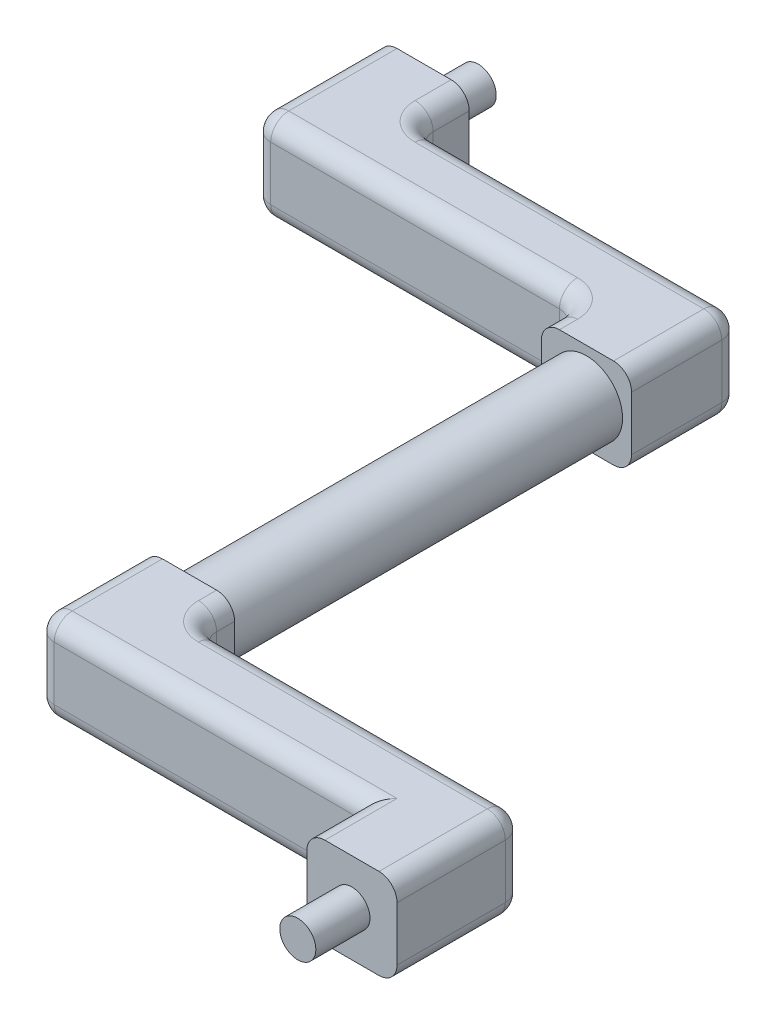
SolidWorks part; units mm, degrees
ref_plane "Alzado" through (0, 0, 0) normal (0, 0, 1) x (1, 0, 0)
ref_plane "Planta" through (0, 0, 0) normal (0, 1, 0) x (1, 0, 0)
ref_plane "Vista lateral" through (0, 0, 0) normal (1, 0, 0) x (0, 0, -1)
sketch "Croquis3" plane through (0, 0, 0) normal (0, 0, 1) x (1, 0, 0)
  circle A0 centre (0, 0) radius 12.7
  dimension "D1" = 25.4
extrude "Saliente-Extruir1" add sketch "Croquis3" against normal blind 88.9 and the other way blind 50.8
sketch "Croquis4" plane through (0, 0, -88.9) normal (0, 0, -1) x (-1, 0, 0)
  line L5 (-15.875, 15.875) -> (15.875, 15.875)
  line L6 (-15.875, 15.875) -> (-15.875, -15.875)
  line L7 (-15.875, -15.875) -> (15.875, -15.875)
  line L8 (15.875, 15.875) -> (15.875, -15.875)
  line L9 (-15.875, 15.875) -> (15.875, -15.875) construction
  line L10 (-15.875, -15.875) -> (15.875, 15.875) construction
  point P0 (0, 0)
  point P1 (0, 0)
  dimension "D1" = 31.75
  dimension "D2" = 31.75
extrude "Saliente-Extruir2" add sketch "Croquis4" along normal blind 38.1
sketch "Croquis6" plane through (-15.875, 0, 0) normal (-1, 0, 0) x (0, 0, 1)
  line L0 (-127, 15.875) -> (-88.9, 15.875) construction
  line L1 (-127, -15.875) -> (-101.6, -15.875)
  line L2 (-127, -15.875) -> (-127, 15.875)
  line L3 (-127, 15.875) -> (-101.6, 15.875)
  line L4 (-101.6, -15.875) -> (-101.6, 15.875)
  dimension "D1" = 25.4
extrude "Saliente-Extruir3" add sketch "Croquis6" along normal blind 114.3
sketch "Croquis8" plane through (0, 0, -127) normal (0, 0, -1) x (-1, 0, 0)
  line L0 (130.175, 15.875) -> (15.875, 15.875) construction
  line L1 (130.175, -15.875) -> (98.425, -15.875)
  line L2 (130.175, -15.875) -> (130.175, 15.875)
  line L3 (130.175, 15.875) -> (98.425, 15.875)
  line L4 (98.425, -15.875) -> (98.425, 15.875)
  dimension "D1" = 31.75
extrude "Saliente-Extruir4" add sketch "Croquis8" along normal blind 19.05
sketch "Croquis9" plane through (0, 0, -146.05) normal (0, 0, -1) x (-1, 0, 0)
  line L0 (130.175, 15.875) -> (98.425, 15.875) construction
  line L1 (98.425, 15.875) -> (98.425, -15.875) construction
  line L2 (98.425, 0) -> (130.175, 0) construction
  line L3 (130.175, -15.875) -> (130.175, 15.875) construction
  line L4 (114.3, 15.875) -> (114.3, -15.875) construction
  line L5 (98.425, -15.875) -> (130.175, -15.875) construction
  circle A0 centre (114.3, 0) radius 6.35
  dimension "D1" = 12.7
extrude "Saliente-Extruir5" add sketch "Croquis9" along normal blind 19.05
fillet "Redondeo1" radius 6.35 16 edges at (-98.425, -15.875, -136.525) (-15.875, -15.875, -95.25) (-98.425, 15.875, -136.525) (-130.175, 15.875, -123.825) (-130.175, -15.875, -123.825) (-41.275, -15.875, -127) (-73.025, -15.875, -101.6) (-41.275, 15.875, -127) (-130.175, 0, -101.6) (-98.425, 0, -127) (-15.875, 0, -101.6) (15.875, 0, -127) (15.875, 15.875, -107.95) (15.875, -15.875, -107.95) (-73.025, 15.875, -101.6) (-15.875, 15.875, -95.25)
ref_plane "Plano1" through (0, 0, -76.2) normal (0, 0, 1) x (1, 0, 0)
sketch "Croquis12" plane through (0, 0, 50.8) normal (0, 0, 1) x (1, 0, 0)
  line L1 (-15.875, 15.875) -> (15.875, 15.875)
  line L2 (-15.875, 15.875) -> (-15.875, -15.875)
  line L3 (-15.875, -15.875) -> (15.875, -15.875)
  line L4 (15.875, 15.875) -> (15.875, -15.875)
  line L5 (-15.875, 15.875) -> (15.875, -15.875) construction
  line L6 (-15.875, -15.875) -> (15.875, 15.875) construction
  point P0 (0, 0)
  dimension "D1" = 31.75
  dimension "D2" = 31.75
extrude "Saliente-Extruir6" add sketch "Croquis12" along normal blind 38.1
sketch "Croquis13" plane through (15.875, 0, 0) normal (1, 0, 0) x (0, 0, -1)
  line L0 (-88.9, -15.875) -> (-50.8, -15.875) construction
  line L1 (-88.9, 15.875) -> (-63.5, 15.875)
  line L2 (-88.9, 15.875) -> (-88.9, -15.875)
  line L3 (-88.9, -15.875) -> (-63.5, -15.875)
  line L4 (-63.5, 15.875) -> (-63.5, -15.875)
  dimension "D1" = 25.4
extrude "Saliente-Extruir7" add sketch "Croquis13" along normal blind 114.3
sketch "Croquis14" plane through (0, 0, 88.9) normal (0, 0, 1) x (1, 0, 0)
  line L0 (-15.875, -15.875) -> (130.175, -15.875) construction
  line L1 (130.175, 15.875) -> (98.425, 15.875)
  line L2 (130.175, 15.875) -> (130.175, -15.875)
  line L3 (130.175, -15.875) -> (98.425, -15.875)
  line L4 (98.425, 15.875) -> (98.425, -15.875)
  dimension "D1" = 31.75
extrude "Saliente-Extruir8" add sketch "Croquis14" along normal blind 19.05
sketch "Croquis16" plane through (0, 0, 107.95) normal (0, 0, 1) x (1, 0, 0)
  line L0 (98.425, 0) -> (134.9944, 0) construction
  line L1 (98.425, 15.875) -> (98.425, -15.875) construction
  line L2 (114.3, 15.875) -> (114.3, -24.0662) construction
  line L3 (130.175, 15.875) -> (98.425, 15.875) construction
  circle A0 centre (114.3, 0) radius 6.35
  dimension "D1" = 12.7
extrude "Saliente-Extruir9" add sketch "Croquis16" along normal blind 19.05
fillet "Redondeo2" radius 6.35 15 edges at (15.875, 0, 63.5) (-15.875, 15.875, 69.85) (-15.875, -15.875, 69.85) (-15.875, 0, 88.9) (41.275, -15.875, 88.9) (98.425, -15.875, 98.425) (98.425, 15.875, 98.425) (130.175, -15.875, 85.725) (130.175, 15.875, 85.725) (73.025, 15.875, 63.5) (73.025, -15.875, 63.5) (41.275, 15.875, 88.9) (130.175, 0, 63.5) (15.875, -15.875, 57.15) (15.875, 15.875, 57.15)
